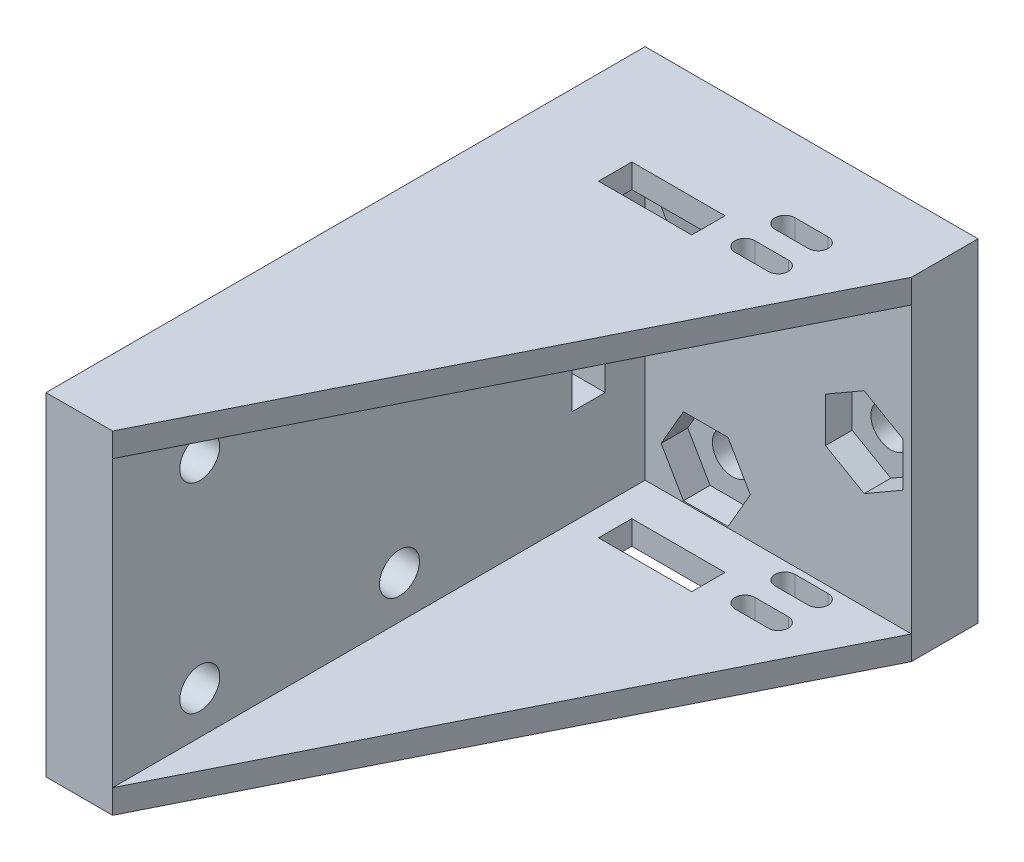
SolidWorks part; units mm, degrees
ref_plane "Front Plane" through (0, 0, 0) normal (0, 0, 1) x (1, 0, 0)
ref_plane "Top Plane" through (0, 0, 0) normal (0, 1, 0) x (1, 0, 0)
ref_plane "Right Plane" through (0, 0, 0) normal (1, 0, 0) x (0, 0, -1)
sketch "Sketch1" plane through (0, 0, 0) normal (0, 0, 1) x (1, 0, 0)
  line L1 (-45.175, -12.5) -> (-20.175, -12.5)
  line L2 (-45.175, -12.5) -> (-45.175, 12.5)
  line L3 (-45.175, 12.5) -> (-20.175, 12.5)
  line L4 (-20.175, -12.5) -> (-20.175, 12.5)
  line L5 (-45.175, -12.5) -> (-20.175, 12.5) construction
  line L6 (-45.175, 12.5) -> (-20.175, -12.5) construction
  circle A0 centre (-35.625, 7.7) radius 1.5 construction
  circle A1 centre (-35.625, 7.7) radius 1.5
  circle A2 centre (-35.625, -7.7) radius 1.5 construction
  circle A3 centre (-35.625, -7.7) radius 1.5
  circle A4 centre (-23.725, 0) radius 1.5 construction
  circle A5 centre (-23.725, 0) radius 1.5
  point P0 (-32.675, 0)
  dimension "D1" = 25
extrude "Boss-Extrude1" add sketch "Sketch1" along normal blind 5
sketch "Sketch2" plane through (0, 0, 5) normal (0, 0, 1) x (1, 0, 0)
  line L0 (-45.175, -12.5) -> (-20.175, -12.5) construction
  line L1 (-45.175, 12.5) -> (-40.175, 12.5)
  line L2 (-45.175, 12.5) -> (-45.175, -12.5)
  line L3 (-45.175, -12.5) -> (-40.175, -12.5)
  line L4 (-40.175, 12.5) -> (-40.175, -12.5)
  dimension "D1" = 5
extrude "Boss-Extrude2" add sketch "Sketch2" along normal blind 40
sketch "Sketch3" plane through (0, 0, 5) normal (0, 0, 1) x (1, 0, 0)
  line L0 (-20.175, 12.5) -> (-40.175, 12.5) construction
  line L1 (-37.2993, 4.8) -> (-33.9507, 4.8)
  line L2 (-33.9507, 4.8) -> (-32.2764, 7.7)
  line L3 (-32.2764, 7.7) -> (-33.9507, 10.6)
  line L4 (-33.9507, 10.6) -> (-37.2993, 10.6)
  line L5 (-37.2993, 10.6) -> (-38.9736, 7.7)
  line L6 (-38.9736, 7.7) -> (-37.2993, 4.8)
  line L7 (-33.9507, -4.8) -> (-37.2993, -4.8)
  line L8 (-37.2993, -4.8) -> (-38.9736, -7.7)
  line L9 (-38.9736, -7.7) -> (-37.2993, -10.6)
  line L10 (-37.2993, -10.6) -> (-33.9507, -10.6)
  line L11 (-33.9507, -10.6) -> (-32.2764, -7.7)
  line L12 (-32.2764, -7.7) -> (-33.9507, -4.8)
  line L13 (-23.725, -3.3486) -> (-20.825, -1.6743)
  line L14 (-20.825, -1.6743) -> (-20.825, 1.6743)
  line L15 (-20.825, 1.6743) -> (-23.725, 3.3486)
  line L16 (-23.725, 3.3486) -> (-26.625, 1.6743)
  line L17 (-26.625, 1.6743) -> (-26.625, -1.6743)
  line L18 (-26.625, -1.6743) -> (-23.725, -3.3486)
  line L19 (-20.175, -12.5) -> (-20.175, 12.5) construction
  circle A0 centre (-35.625, 7.7) radius 2.9 construction
  circle A1 centre (-35.625, -7.7) radius 2.9 construction
  circle A2 centre (-23.725, 0) radius 2.9 construction
  dimension "D1" = 5.8
extrude "Cut-Extrude1" cut sketch "Sketch3" against normal blind 2
sketch "Sketch4" plane through (0, -12.5, 0) normal (0, -1, 0) x (1, 0, 0)
  line L0 (-40.175, 45) -> (-20.175, 5)
  line L1 (-20.175, 5) -> (-40.175, 5)
  line L2 (-40.175, 5) -> (-40.175, 45)
extrude "Boss-Extrude3" add sketch "Sketch4" against normal blind 1.8
sketch "Sketch5" plane through (0, 12.5, 0) normal (0, 1, 0) x (1, 0, 0)
  line L3 (-40.175, -45) -> (-20.175, -5)
  line L4 (-20.175, -5) -> (-40.175, -5)
  line L5 (-40.175, -5) -> (-40.175, -45)
  line L6 (-40.175, -45) -> (-20.175, -5)
  line L7 (-20.175, -5) -> (-40.175, -5)
  line L8 (-40.175, -5) -> (-40.175, -45)
  dimension "D1" = 0
extrude "Boss-Extrude4" add sketch "Sketch5" against normal blind 1.8
sketch "Sketch6" plane through (0, 12.5, 0) normal (0, 1, 0) x (1, 0, 0)
  line L0 (-40.175, -5) -> (-20.175, -5) construction
  line L1 (-40.175, -5) -> (-20.175, -5)
  line L3 (-38.175, -8) -> (-31.175, -8)
  line L4 (-38.175, -8) -> (-38.175, -10.5)
  line L5 (-38.175, -10.5) -> (-31.175, -10.5)
  line L6 (-31.175, -8) -> (-31.175, -10.5)
  dimension "D1" = 7
  dimension "D2" = 2.5
  dimension "D3" = 2
  dimension "D4" = 3
extrude "Cut-Extrude2" cut sketch "Sketch6" against normal through all contours L6 L3 L4 L5
sketch "Sketch7" plane through (-40.175, 0, 0) normal (1, 0, 0) x (0, 0, -1)
  line L0 (-10.5, 10.7) -> (-8, 10.7) construction
  line L1 (-10.5, 10.7) -> (-8, 10.7) construction
  line L2 (-45, 0) -> (-10.5, 0) construction
  line L3 (-10.5, 3.5) -> (-8, 3.5)
  line L4 (-10.5, 3.5) -> (-10.5, -3.5)
  line L5 (-10.5, -3.5) -> (-8, -3.5)
  line L6 (-8, 3.5) -> (-8, -3.5)
  line L7 (-45, -10.7) -> (-45, 10.7) construction
  line L8 (-10.5, 3.5) -> (-10.5, 10.7) construction
  dimension "D1" = 7
  dimension "D2" = 2.5
extrude "Cut-Extrude3" cut sketch "Sketch7" against normal through all
sketch "Sketch8" plane through (0, -12.5, 0) normal (0, -1, 0) x (1, 0, 0)
  line L0 (-20.175, 5) -> (-40.175, 5) construction
  line L1 (-20.175, 5) -> (-40.175, 5)
  line L2 (-27.175, 5) -> (-27.175, 25.3759) construction
  line L3 (-28.425, 6.25) -> (-25.925, 6.25) construction
  line L4 (-28.425, 7) -> (-25.925, 7)
  line L5 (-28.425, 5.5) -> (-25.925, 5.5)
  line L6 (-25.925, 9.25) -> (-28.425, 9.25) construction
  line L7 (-25.925, 8.5) -> (-28.425, 8.5)
  line L8 (-25.925, 10) -> (-28.425, 10)
  line L9 (-31.175, 8) -> (-31.175, 10.5) construction
  arc A0 (-28.425, 7) -> (-28.425, 5.5) centre (-28.425, 6.25) ccw
  arc A1 (-25.925, 5.5) -> (-25.925, 7) centre (-25.925, 6.25) ccw
  arc A2 (-25.925, 8.5) -> (-25.925, 10) centre (-25.925, 9.25) ccw
  arc A3 (-28.425, 10) -> (-28.425, 8.5) centre (-28.425, 9.25) ccw
  point P6 (-27.175, 6.25)
  point P12 (-27.175, 9.25)
  dimension "D1" = 4
  dimension "D2" = 0.5
  dimension "D3" = 1.5
  dimension "D4" = 3
  dimension "D5" = 4
extrude "Cut-Extrude4" cut sketch "Sketch8" against normal through all contours L8 A3 L7 A2 | L5 A1 L4 A0
sketch "Sketch9" plane through (-45.175, 0, 0) normal (-1, 0, 0) x (0, 0, 1)
  line L0 (18.45, 23.7845) -> (18.45, -33.9363) construction
  line L1 (15.45, -13.4) -> (15.45, 13.4) construction
  line L2 (21.95, 23.7845) -> (21.95, -22.2084) construction
  line L3 (21.95, 7.5) -> (49.7465, 7.5) construction
  line L5 (21.95, -7.5) -> (49.4161, -7.5) construction
  line L6 (45, 12.5) -> (0, 12.5) construction
  line L7 (45, -12.5) -> (0, -12.5) construction
  circle A0 centre (23.45, 7.5) radius 1.5
  circle A1 centre (23.45, -7.5) radius 1.5
  circle A2 centre (38.45, 7.5) radius 1.5
  circle A3 centre (38.45, -7.5) radius 1.5
  dimension "D3" = 3
  dimension "D1" = 3
  dimension "D2" = 3.5
  dimension "D4" = 5
  dimension "D5" = 15
  dimension "D6" = 5
  dimension "D7" = 15
extrude "Cut-Extrude5" cut sketch "Sketch9" against normal through all
